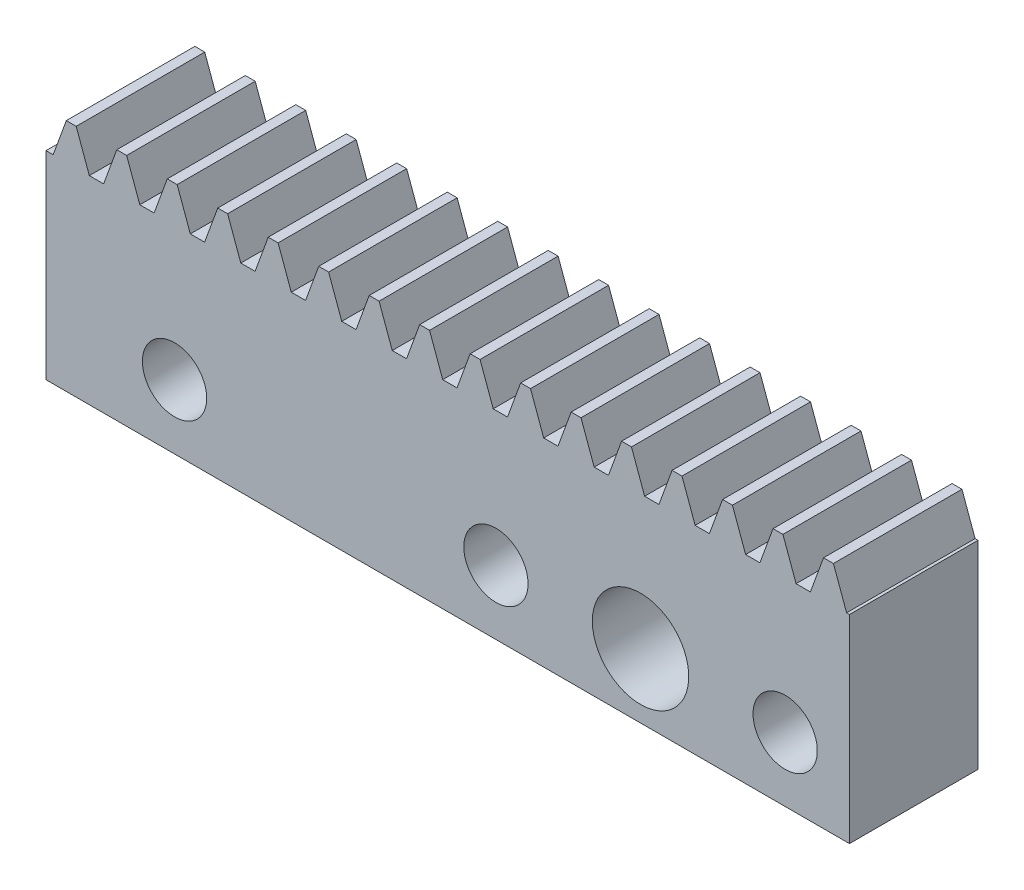
SolidWorks part; units mm, degrees
extrude "Blank" add sketch "BlankSke" against normal blind 4
sketch "BlankSke" plane through (0, 0, 0) normal (0, 0, 1) x (1, 0, 0)
  line L1 (0, 0) -> (25, 0)
  line L2 (0, 0) -> (0, 7.3)
  line L3 (0, 7.3) -> (25, 7.3)
  line L4 (25, 0) -> (25, 7.3)
  dimension "Length" = 25
  dimension "Blank_height" = 7.3
ref_plane "Plane1" through (0, 0, 0) normal (0, 0, 1) x (1, 0, 0)
ref_plane "Plane2" through (0, 0, 0) normal (0, 1, 0) x (1, 0, 0)
ref_plane "Plane3" through (0, 0, 0) normal (1, 0, 0) x (0, 0, -1)
sketch "HoldingSke" plane through (0, 0, 0) normal (0, 1, 0) x (1, 0, 0)
  line L0 (0, 0) -> (0.2783, 1.9805)
  line L1 (-15, 0) -> (100, 0) construction
  line L2 (0, 0) -> (-2.1039, 2.3779)
  line L3 (0, 0) -> (-11.863, 4.5341)
  line L4 (0, 0) -> (8.2587, 2.5249)
  line L5 (0, 0) -> (-23.7986, -8.8762)
  line L6 (0, 0) -> (-10.5278, -7.1032)
  line L9 (-71.009, 38.7566) -> (-47.5167, 47.3071)
  line L10 (-76.2, 2.8779) -> (-69.4, 2.8779)
  line L11 (0, 0) -> (-4, 0)
  line L12 (-76.2, 101.6) -> (-76.181, 101.6)
  line L13 (24.9733, 27.94) -> (52.9518, 28.4284)
  line L14 (24.9733, 27.94) -> (24.9743, 27.94)
  line L15 (24.9733, 27.94) -> (100.4006, 29.5858)
  circle A0 centre (0, 0) radius 19.05
  circle A1 centre (0, 0) radius 3.4
  circle A2 centre (0, 0) radius 12.7
  dimension "MPH" = 6.8
  dimension "Diameter" = 38.1
  dimension "Num_teeth" = 17
  dimension "Pitch" = 2
  dimension "Show_teeth" = 998
  dimension "Thickness" = 12.7
  dimension "Ap" = 20
  dimension "Pitch_height" = 6.8
  dimension "Width" = 4
  dimension "Backlash" = 0.019
  dimension "Addendum_fac" = 1
  dimension "Dedendum_fac" = 1.25
  dimension "Clearance_fac" = 0.25
  dimension "Dedendum_add" = 0.001
  dimension "Length" = 25
  dimension "Module" = 0.5
sketch "TooCutSkeIll" plane through (0, 0, 0) normal (0, 0, 1) x (1, 0, 0)
  line L0 (-0.6269, 7.2868) -> (-0.2524, 6.2579)
  line L1 (-0.134, 6.175) -> (0.134, 6.175)
  line L2 (0.2524, 6.2579) -> (0.6269, 7.2868)
  line L3 (25, 7.3) -> (0, 7.3) construction
  line L4 (0, 0) -> (0, 64.897) construction
  line L5 (-13.208, 6.8) -> (12.954, 6.8) construction
  line L6 (0, 0) -> (25, 0) construction
  line L7 (0.4497, 6.8) -> (0.4497, 48.7463) construction
  line L8 (-0.4497, 6.8) -> (-0.4497, 48.7463) construction
  line L9 (0.6457, 7.3) -> (0.6457, 7.3254)
  line L10 (-0.6457, 7.3) -> (-0.6457, 7.3254)
  line L11 (-0.6457, 7.3254) -> (0.6457, 7.3254)
  arc A0 (0.134, 6.175) -> (0.2524, 6.2579) centre (0.134, 6.301) ccw
  arc A1 (-0.2524, 6.2579) -> (-0.134, 6.175) centre (-0.134, 6.301) ccw
  arc A2 (0.6457, 7.3) -> (0.6269, 7.2868) centre (0.6457, 7.28) ccw
  arc A3 (-0.6269, 7.2868) -> (-0.6457, 7.3) centre (-0.6457, 7.28) ccw
  dimension "Pitch_height" = 6.8
  dimension "Addendum_plus" = 0.5254
  dimension "Pressure_angle" = 20
  dimension "Gap_width" = 0.8994
  dimension "Dedendum" = 0.625
extrude "ToothCutIll" [suppressed] cut sketch "TooCutSkeIll" against normal through all
sketch "TooCutSkeSim" plane through (0, 0, 0) normal (0, 0, 1) x (1, 0, 0)
  line L0 (0.2222, 6.175) -> (-0.2222, 6.175)
  line L1 (0.6409, 7.3254) -> (0.2222, 6.175)
  line L2 (0, 17.4625) -> (0, 53.467) construction
  line L3 (0.6409, 7.3254) -> (-0.6409, 7.3254)
  line L6 (-0.6409, 7.3254) -> (-0.2222, 6.175)
  line L9 (-0.4497, 6.8) -> (0.4497, 6.8) construction
  line L10 (0, 0) -> (25, 0) construction
  line L11 (0.4497, 6.8) -> (0.4497, 53.467) construction
  line L12 (-0.4497, 6.8) -> (-0.4497, 53.467) construction
  dimension "Pitch_height" = 6.8
  dimension "Addendum_plus" = 0.5254
  dimension "Pressure_angle" = 20
  dimension "Gap_width" = 0.8994
  dimension "Dedendum" = 0.625
extrude "ToothCutSim" cut sketch "TooCutSkeSim" against normal through all
pattern_linear "TeethCuts" count 17 spacing 1.5708 along (1, 0, 0) of "ToothCutIll", "ToothCutSim"
sketch "Sketch1" plane through (0, 0, -4) normal (0, 0, -1) x (-1, 0, 0)
  line L0 (-23, 2) -> (-25, 2)
  line L2 (-25, 0) -> (-25, 6.175) construction
  line L3 (-23, 0) -> (-23, 1)
  line L4 (0, 0) -> (-25, 0) construction
  line L5 (-23, 1) -> (-23, 3)
  line L6 (-22, 2) -> (-20, 2)
  line L7 (-20, 2) -> (-17, 2)
  line L8 (-17, 2) -> (-15, 2)
  line L9 (-15, 2) -> (-13, 2)
  line L10 (-13, 2) -> (-5, 2)
  line L11 (-5, 2) -> (-3, 2)
  circle A1 centre (-23, 2) radius 1
  circle A2 centre (-18.5, 2) radius 1.5
  circle A3 centre (-14, 2) radius 1
  circle A4 centre (-4, 2) radius 1
extrude "Cut-Extrude1" cut sketch "Sketch1" against normal through all contours L0 A1 L5 | A1 L5 | L5 A1 L0 | L7 A2 | L7 A2 | L9 A3 | L9 A3 | L11 A4 | L11 A4
equation "' \"Module@HoldingSke\" = 6.35"
equation "' \"Num_teeth@HoldingSke\" = 12"
equation "' \"Ap@HoldingSke\" =  20"
equation "' \"Ap@HoldingSke\" = 20"
equation "' \"Width@HoldingSke\" = 0.25 * 25.4"
equation "' \"Show_teeth@HoldingSke\" = 500"
equation "' \"Backlash@HoldingSke\" = 0.009 * 25.4"
equation "' \"Addendum_fac@HoldingSke\" = 1.0"
equation "' \"Dedendum_fac@HoldingSke\" = 1.25"
equation "' \"Dedendum_add@HoldingSke\" = 0.00005 * 25.4"
equation "' \"Clearance_fac@HoldingSke\" = 0.25"
equation "' \"Pitch_height@HoldingSke\" = 1 * 25.4"
equation "' \"Length@HoldingSke\" = 4.71 * 25.4"
equation "\"Pitch@HoldingSke\" = 1 / \"Module@HoldingSke\""
equation "\"MPH@HoldingSke\" = \"Dedendum_fac@HoldingSke\" / \"Pitch@HoldingSke\" + 2 * \"Dedendum_add@HoldingSke\" + 0.002 * 25.4"
equation "\"MPH@HoldingSke\" = ((sgn( \"MPH@HoldingSke\" - \"Pitch_height@HoldingSke\")+1)*( \"MPH@HoldingSke\" - \"Pitch_height@HoldingSke\"))/2 + \"Pitch_height@HoldingSke\""
equation "\"Blank_height@BlankSke\" = \"Pitch_height@HoldingSke\" + \"Addendum_fac@HoldingSke\"  / \"Pitch@HoldingSke\" "
equation "\"Length@BlankSke\" =  \"Length@HoldingSke\""
equation "\"Face_width@Blank\" = \"Width@HoldingSke\""
equation "\"Pressure_angle@TooCutSkeIll\" = \"Ap@HoldingSke\""
equation "\"Addendum_plus@TooCutSkeIll\" =  \"Addendum_fac@HoldingSke\"  / \"Pitch@HoldingSke\" + 0.001 *25.4"
equation "\"Dedendum@TooCutSkeIll\" = \"Dedendum_fac@HoldingSke\"  / \"Pitch@HoldingSke\""
equation "\"Pitch_height@TooCutSkeIll\" =  \"MPH@HoldingSke\""
equation "\"Gap_width@TooCutSkeIll\" = 3.14159265 / 2 / \"Pitch@HoldingSke\" + 6 * \"Backlash@HoldingSke\""
equation "\"Pressure_angle@TooCutSkeSim\" = \"Ap@HoldingSke\""
equation "\"Addendum_plus@TooCutSkeSim\" =  \"Addendum_fac@HoldingSke\"  / \"Pitch@HoldingSke\" + 0.001 * 25.4"
equation "\"Dedendum@TooCutSkeSim\" = \"Dedendum_fac@HoldingSke\"  / \"Pitch@HoldingSke\""
equation "\"Pitch_height@TooCutSkeSim\" =  \"MPH@HoldingSke\""
equation "\"Gap_width@TooCutSkeSim\" = 3.14159265 / 2 / \"Pitch@HoldingSke\" + 6 * \"Backlash@HoldingSke\""
equation "\"Root_fillet@TooCutSkeIll\" = \"Clearance_fac@HoldingSke\" / \"Pitch@HoldingSke\" + \"Dedendum_add@HoldingSke\""
equation "\"Break_rad@TooCutSkeIll\" = 0.02 / \"Pitch@HoldingSke\" * 2"
equation "\"Linear_pitch@TeethCuts\" = 3.14159265 / \"Pitch@HoldingSke\""
equation "\"Num_teeth@HoldingSke\" = int( ( \"Length@HoldingSke\" + 0 ) / (3.14159265 / \"Pitch@HoldingSke\")) + 0.9999  + 1"
equation " \"Num_teeth@TeethCuts\" = int( \"Show_teeth@HoldingSke\" ) + 1"
equation " \"Num_teeth@TeethCuts\" = ((sgn( \"Num_teeth@TeethCuts\" - \"Num_teeth@HoldingSke\" )-1)*( \"Num_teeth@TeethCuts\" - \"Num_teeth@HoldingSke\" ))/-2+ \"Num_teeth@HoldingSke\""
equation " \"Num_teeth@TeethCuts\" = ((sgn( \"Num_teeth@TeethCuts\" - 2.0)+1)*( \"Num_teeth@TeethCuts\" - 2.0))/2 +2.0"
